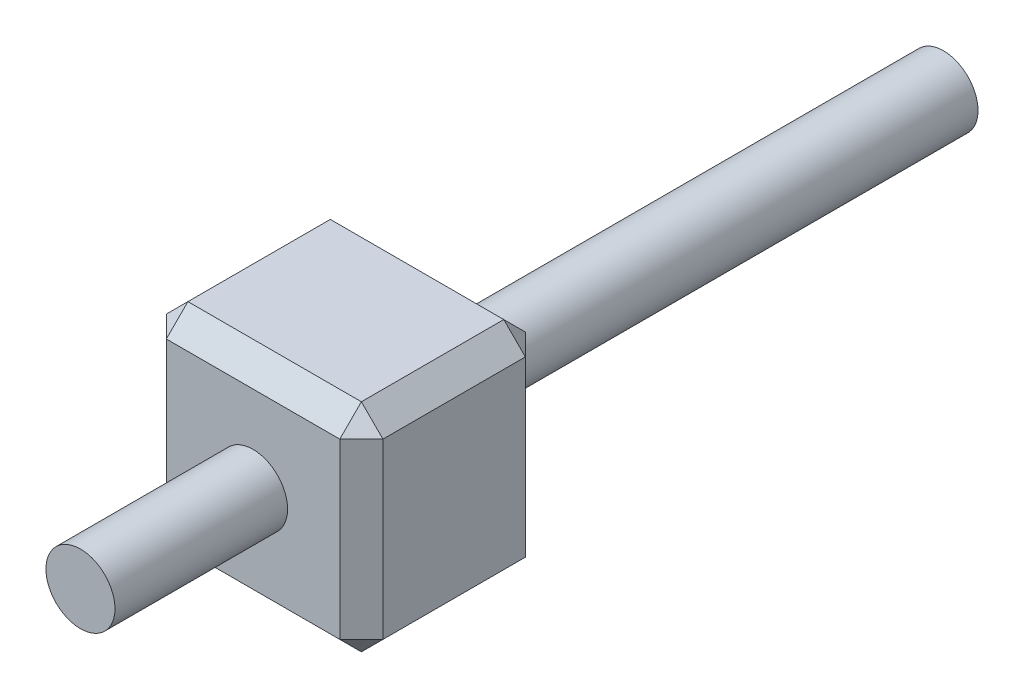
SolidWorks part; units mm, degrees
ref_plane "Face" through (0, 0, 0) normal (0, 0, 1) x (1, 0, 0)
ref_plane "Dessus" through (0, 0, 0) normal (0, 1, 0) x (1, 0, 0)
ref_plane "Droite" through (0, 0, 0) normal (1, 0, 0) x (0, 0, -1)
sketch "Esquisse1" plane through (0, 0, 0) normal (0, 0, 1) x (1, 0, 0)
  line L0 (-29.2454, 24.3197) -> (-29.2454, 21.8097) construction
  line L1 (-30.5004, 24.3197) -> (-27.9904, 24.3197)
  line L2 (-30.5004, 24.3197) -> (-30.5004, 21.8097)
  line L3 (-30.5004, 21.8097) -> (-27.9904, 21.8097)
  line L4 (-27.9904, 24.3197) -> (-27.9904, 21.8097)
  dimension "D1" = 2.51
  dimension "D2" = 2.51
extrude "Extrusion1" add sketch "Esquisse1" along normal blind 2.15
sketch "Esquisse2" plane through (0, 0, 2.15) normal (0, 0, 1) x (1, 0, 0)
  line L0 (-29.2454, 24.3197) -> (-29.2454, 21.8097) construction
  line L1 (-27.9904, 24.3197) -> (-30.5004, 24.3197) construction
  line L2 (-30.5004, 21.8097) -> (-27.9904, 21.8097) construction
  circle A0 centre (-29.2454, 23.0647) radius 0.4
  dimension "D1" = 0.8
extrude "Extrusion2" add sketch "Esquisse2" along normal blind 2 and the other way blind 8
chamfer "Chanfrein1" distance 0.25 angle 45 12 edges at (-30.5004, 23.0647, 2.15) (-30.5004, 23.0647, 0) (-30.5004, 21.8097, 1.075) (-29.2454, 21.8097, 2.15) (-29.2454, 21.8097, 0) (-27.9904, 21.8097, 1.075) (-27.9904, 23.0647, 2.15) (-27.9904, 23.0647, 0) (-27.9904, 24.3197, 1.075) (-29.2454, 24.3197, 2.15) (-30.5004, 24.3197, 1.075) (-29.2454, 24.3197, 0)
